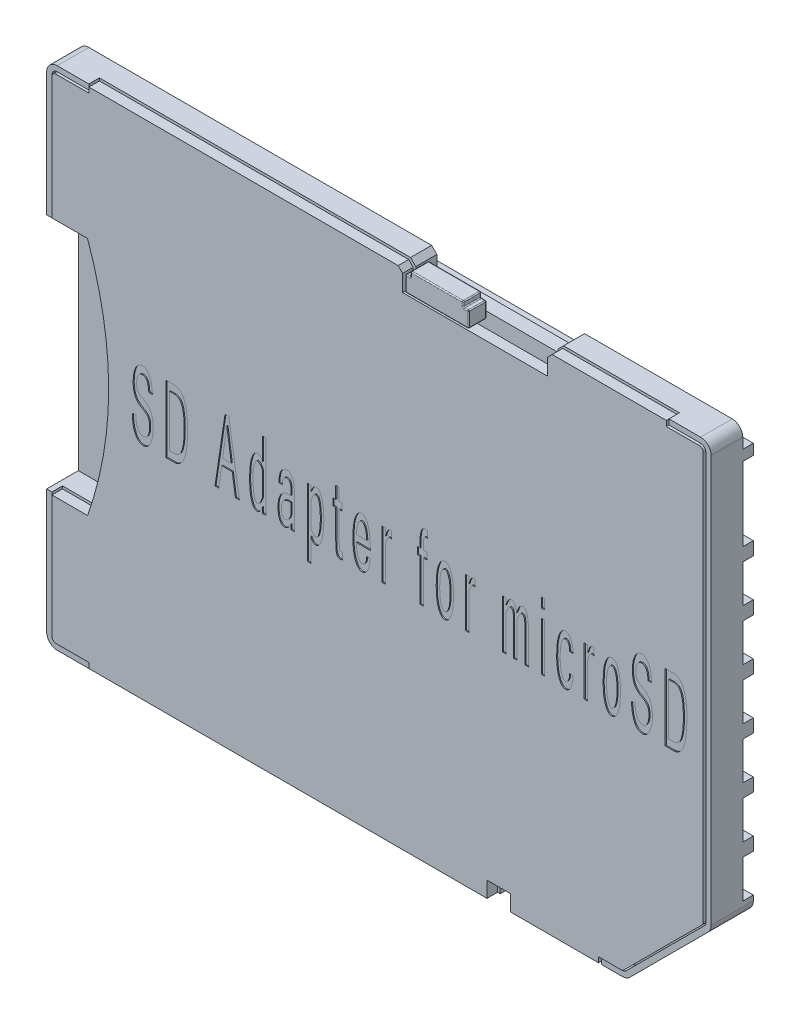
SolidWorks part; units mm, degrees
ref_plane "Front Plane" through (0, 0, 0) normal (0, 0, 1) x (1, 0, 0)
ref_plane "Top Plane" through (0, 0, 0) normal (0, 1, 0) x (1, 0, 0)
ref_plane "Right Plane" through (0, 0, 0) normal (1, 0, 0) x (0, 0, -1)
sketch "Sketch1" plane through (0, 0, 0) normal (0, 0, 1) x (1, 0, 0)
  line L0 (6.25, 0) -> (6.25, 0.75)
  line L1 (15.75, 24) -> (15.75, 4)
  line L2 (-15.75, 0) -> (-15.75, 24)
  line L3 (11.75, 0) -> (6.25, 0)
  line L4 (6.25, 0.75) -> (5.25, 0.75)
  line L5 (15.75, 4) -> (11.75, 0)
  line L6 (5.25, 0.75) -> (5.25, 0)
  line L7 (5.25, 0) -> (-15.75, 0)
  line L8 (-15.75, 24) -> (15.75, 24)
extrude "Boss-Extrude1" add sketch "Sketch1" along normal blind 2
fillet "Fillet1" radius 0.5 5 edges at (-15.75, 0, 1) (-15.75, 24, 1) (15.75, 24, 1) (11.75, 0, 1) (15.75, 4, 1)
sketch "Sketch2" plane through (0, 0, 0) normal (0, 0, -1) x (-1, 0, 0)
  line L0 (15.75, 23) -> (15.75, 23.5)
  line L2 (0, 23) -> (15.75, 23)
  line L3 (15.75, 23.5) -> (15.75, 0.5) construction
  line L4 (0, 23) -> (-15.75, 23)
  line L5 (-15.75, 4.2071) -> (-15.75, 23.5) construction
  line L6 (-15.75, 23) -> (-15.75, 23.5)
  line L10 (15.25, 24) -> (-15.25, 24)
  line L11 (15.25, 24) -> (-15.25, 24)
  arc A6 (15.75, 23.5) -> (15.25, 24) centre (15.25, 23.5) ccw
  arc A7 (-15.25, 24) -> (-15.75, 23.5) centre (-15.25, 23.5) ccw
  arc A8 (15.75, 23.5) -> (15.25, 24) centre (15.25, 23.5) ccw
  arc A9 (-15.25, 24) -> (-15.75, 23.5) centre (-15.25, 23.5) ccw
  dimension "D1" = 0
extrude "Cut-Extrude1" cut sketch "Sketch2" against normal blind 0.5
sketch "Sketch3" plane through (0, 0, 0) normal (0, 0, -1) x (-1, 0, 0)
  line L1 (0, 0.75) -> (15.75, 0.75)
  line L2 (15.75, 23) -> (15.75, 0.5) construction
  line L3 (15.75, 0.75) -> (15.75, 0.5)
  line L4 (0, 0.75) -> (-12.5, 0.75)
  line L5 (-11.8964, 0.1464) -> (-15.6036, 3.8536) construction
  line L6 (-12.5, 0.75) -> (-11.8964, 0.1464)
  line L18 (15.25, 0) -> (-5.25, 0)
  line L19 (15.25, 0) -> (-5.25, 0)
  line L20 (-6.25, 0) -> (-5.25, 0)
  line L21 (-11.5429, 0) -> (-6.25, 0)
  line L22 (-11.5429, 0) -> (-6.25, 0)
  arc A16 (15.25, 0) -> (15.75, 0.5) centre (15.25, 0.5) ccw
  arc A17 (15.25, 0) -> (15.75, 0.5) centre (15.25, 0.5) ccw
  arc A20 (-11.8964, 0.1464) -> (-11.5429, 0) centre (-11.5429, 0.5) ccw
  arc A21 (-11.8964, 0.1464) -> (-11.5429, 0) centre (-11.5429, 0.5) ccw
  dimension "D1" = 0
  dimension "D2" = 0
extrude "Cut-Extrude2" cut sketch "Sketch3" against normal blind 0.5
sketch "Sketch4" plane through (0, 0, 2) normal (0, 0, 1) x (1, 0, 0)
  line L0 (1.25, 23.25) -> (8, 23.25)
  line L1 (1.25, 24) -> (1.25, 23.25)
  line L2 (15.25, 24) -> (-15.25, 24) construction
  line L3 (8, 23.25) -> (8, 24)
  line L4 (1.25, 24) -> (8, 24)
extrude "Cut-Extrude3" cut sketch "Sketch4" against normal blind 1.5
chamfer "Chamfer1" distance 0.25 angle 45 2 edges at (8, 24, 1.25) (1.25, 24, 1.25)
sketch "Sketch5" plane through (0, 0, 0) normal (0, 0, -1) x (-1, 0, 0)
  line L0 (-15.75, 23) -> (-15.75, 22.5)
  line L1 (-15.75, 4.2071) -> (-15.75, 23) construction
  line L2 (-15.75, 22.5) -> (-10, 22.5)
  line L3 (-10, 22.5) -> (-10, 19)
  line L4 (-10, 19) -> (-15.75, 19)
  line L5 (-15.75, 19) -> (-15.75, 22.5)
  line M5 (-15.75, 23) -> (-15.75, 4.2071)
extrude "Cut-Extrude4" cut sketch "Sketch5" against normal blind 0.5 contours L4 L3 L2 M5
sketch "Sketch9" plane through (0, 0, 0) normal (0, 0, -1) x (-1, 0, 0)
  line L0 (-15.75, 18.375) -> (-15.75, 16.575)
  line L1 (-15.75, 4.2071) -> (-15.75, 19) construction
  line L2 (-15.75, 18.375) -> (-10, 18.375)
  line L3 (-10, 18.375) -> (-10, 16.575)
  line L4 (-10, 16.575) -> (-15.75, 16.575)
  line L5 (-15.75, 6.25) -> (-15.75, 4.45)
  line L6 (-15.75, 15.95) -> (-10, 15.95)
  line L7 (-10, 15.95) -> (-10, 14.15)
  line L8 (-10, 14.15) -> (-15.75, 14.15)
  line L9 (-15.75, 8.675) -> (-15.75, 6.875)
  line L10 (-15.75, 13.525) -> (-10, 13.525)
  line L11 (-10, 13.525) -> (-10, 11.725)
  line L12 (-10, 11.725) -> (-15.75, 11.725)
  line L13 (-15.75, 11.1) -> (-15.75, 9.3)
  line L14 (-15.75, 11.1) -> (-10, 11.1)
  line L15 (-10, 11.1) -> (-10, 9.3)
  line L16 (-10, 9.3) -> (-15.75, 9.3)
  line L17 (-15.75, 13.525) -> (-15.75, 11.725)
  line L18 (-15.75, 8.675) -> (-10, 8.675)
  line L19 (-10, 8.675) -> (-10, 6.875)
  line L20 (-10, 6.875) -> (-15.75, 6.875)
  line L21 (-15.75, 15.95) -> (-15.75, 14.15)
  line L22 (-15.75, 6.25) -> (-10, 6.25)
  line L23 (-10, 6.25) -> (-10, 4.45)
  line L24 (-10, 4.45) -> (-15.75, 4.45)
  line L26 (-15.6, 3.85) -> (-7.75, 3.85)
  line L27 (-7.75, 3.85) -> (-7.75, 2.05)
  line L28 (-7.75, 2.05) -> (-13.8, 2.05)
  line L29 (-12.5, 0.75) -> (-15.6036, 3.8536) construction
  line L30 (-13.8, 2.05) -> (-15.6, 3.85)
  dimension "D1" = 1.8
  dimension "D2" = 1.8
  dimension "D3" = 1.8
  dimension "D4" = 1.8
  dimension "D5" = 1.8
  dimension "D6" = 1.8
  dimension "D7" = 0.625
  dimension "D8" = 0.625
  dimension "D9" = 0.625
  dimension "D10" = 0.625
  dimension "D11" = 0.625
extrude "Cut-Extrude7" cut sketch "Sketch9" against normal blind 0.5
sketch "Sketch10" plane through (0, 0, 0.5) normal (0, 0, -1) x (-1, 0, 0)
  line L6 (-10.125, 22.5) -> (-10.125, 19)
  line L7 (-10.125, 22.375) -> (-10.125, 19.125)
  line L9 (-10.125, 16.575) -> (-10.125, 18.375)
  line L10 (-10.125, 16.7) -> (-10.125, 18.25)
  line L12 (-10.125, 14.15) -> (-10.125, 15.95)
  line L13 (-10.125, 14.275) -> (-10.125, 15.825)
  line L15 (-10.125, 11.725) -> (-10.125, 13.525)
  line L16 (-10.125, 11.85) -> (-10.125, 13.4)
  line L18 (-10.125, 9.3) -> (-10.125, 11.1)
  line L19 (-10.125, 9.425) -> (-10.125, 10.975)
  line L21 (-10.125, 6.875) -> (-10.125, 8.675)
  line L22 (-10.125, 7) -> (-10.125, 8.55)
  line L24 (-10.125, 4.45) -> (-10.125, 6.25)
  line L25 (-10.125, 4.575) -> (-10.125, 6.125)
  line L26 (-14.125, 22.375) -> (-14.125, 19.125)
  line L27 (-7.875, 2.05) -> (-7.875, 3.85)
  line L28 (-7.875, 2.175) -> (-7.875, 3.725)
  line L29 (-14.125, 16.7) -> (-14.125, 18.25)
  line L30 (-14.125, 14.275) -> (-14.125, 15.825)
  line L31 (-14.125, 11.85) -> (-14.125, 13.4)
  line L32 (-14.125, 9.425) -> (-14.125, 10.975)
  line L33 (-14.125, 7) -> (-14.125, 8.55)
  line L34 (-14.125, 4.575) -> (-14.125, 6.125)
  line L37 (-15.75, 22.375) -> (-10, 22.375)
  line L38 (-14.125, 22.375) -> (-10.125, 22.375)
  line L40 (-10, 19.125) -> (-15.75, 19.125)
  line L41 (-10.125, 19.125) -> (-14.125, 19.125)
  line L43 (-10, 18.25) -> (-15.75, 18.25)
  line L44 (-10.125, 18.25) -> (-14.125, 18.25)
  line L46 (-15.75, 16.7) -> (-10, 16.7)
  line L47 (-14.125, 16.7) -> (-10.125, 16.7)
  line L52 (-10, 15.825) -> (-15.75, 15.825)
  line L53 (-10.125, 15.825) -> (-14.125, 15.825)
  line L55 (-15.75, 14.275) -> (-10, 14.275)
  line L56 (-14.125, 14.275) -> (-10.125, 14.275)
  line L58 (-10, 13.4) -> (-15.75, 13.4)
  line L59 (-10.125, 13.4) -> (-14.125, 13.4)
  line L61 (-15.75, 11.85) -> (-10, 11.85)
  line L62 (-14.125, 11.85) -> (-10.125, 11.85)
  line L64 (-10, 10.975) -> (-15.75, 10.975)
  line L65 (-10.125, 10.975) -> (-14.125, 10.975)
  line L67 (-15.75, 9.425) -> (-10, 9.425)
  line L68 (-14.125, 9.425) -> (-10.125, 9.425)
  line L70 (-10, 8.55) -> (-15.75, 8.55)
  line L71 (-10.125, 8.55) -> (-14.125, 8.55)
  line L73 (-15.75, 7) -> (-10, 7)
  line L74 (-14.125, 7) -> (-10.125, 7)
  line L76 (-10, 6.125) -> (-15.75, 6.125)
  line L77 (-10.125, 6.125) -> (-14.125, 6.125)
  line L79 (-15.75, 4.575) -> (-10, 4.575)
  line L80 (-14.125, 4.575) -> (-10.125, 4.575)
  line L82 (-7.75, 3.725) -> (-15.6, 3.725)
  line L83 (-7.875, 3.725) -> (-11.625, 3.725)
  line L84 (-11.625, 2.175) -> (-11.625, 3.725)
  line L85 (-13.8, 2.175) -> (-7.75, 2.175)
  line L86 (-11.625, 2.175) -> (-7.875, 2.175)
  line L88 (-11.625, 2.05) -> (-11.625, 3.85) construction
  line L89 (-7.875, 2.05) -> (-7.875, 3.85) construction
  line L90 (-14.125, 4.45) -> (-14.125, 6.25) construction
  line L91 (-10.125, 4.45) -> (-10.125, 6.25) construction
  line L92 (-14.125, 6.875) -> (-14.125, 8.675) construction
  line L93 (-10.125, 6.875) -> (-10.125, 8.675) construction
  line L94 (-14.125, 9.3) -> (-14.125, 11.1) construction
  line L95 (-10.125, 9.3) -> (-10.125, 11.1) construction
  line L96 (-14.125, 11.725) -> (-14.125, 13.525) construction
  line L97 (-10.125, 11.725) -> (-10.125, 13.525) construction
  line L98 (-14.125, 14.15) -> (-14.125, 15.95) construction
  line L99 (-10.125, 14.15) -> (-10.125, 15.95) construction
  line L100 (-14.125, 16.575) -> (-14.125, 18.375) construction
  line L101 (-10.125, 16.575) -> (-10.125, 18.375) construction
  line L102 (-14.125, 22.5) -> (-14.125, 19) construction
  line L103 (-10.125, 22.5) -> (-10.125, 19) construction
  dimension "D1" = 0.125
  dimension "D2" = 0.125
  dimension "D3" = 0.125
  dimension "D4" = 0.125
  dimension "D5" = 0.125
  dimension "D6" = 0.125
  dimension "D7" = 0.125
  dimension "D8" = 0.125
  dimension "D9" = 4
  dimension "D10" = 4
  dimension "D11" = 0.125
  dimension "D12" = 0.125
  dimension "D13" = 0.125
  dimension "D14" = 0.125
  dimension "D15" = 0.125
  dimension "D16" = 0.125
  dimension "D17" = 0.125
  dimension "D18" = 0.125
  dimension "D19" = 0.125
  dimension "D20" = 0.125
  dimension "D21" = 0.125
  dimension "D22" = 0.125
  dimension "D23" = 0.125
  dimension "D24" = 0.125
  dimension "D25" = 0.125
  dimension "D26" = 0.125
  dimension "D27" = 3.75
extrude "Boss-Extrude2" add sketch "Sketch10" along normal blind 0.05 separate body
sketch "Sketch11" plane through (0, 23.25, 0) normal (0, 1, 0) x (1, 0, 0)
  line L0 (8, -1.9) -> (8, -1.15)
  line L1 (8, -0.5) -> (8, -2) construction
  line L2 (8, -1.9) -> (1.25, -1.9)
  line L3 (1.25, -0.5) -> (1.25, -2) construction
  line L4 (1.25, -1.9) -> (1.25, -1.15)
  line L5 (1.25, -0.5) -> (1.25, -2) construction
  line L6 (1.25, -1.15) -> (8, -1.15)
  line L7 (8, -2) -> (8, -0.5) construction
  line L8 (8, -1.15) -> (8, -1.9)
  line M4 (8, -2) -> (8, -0.5)
  line M6 (1.25, -0.5) -> (1.25, -2)
extrude "Cut-Extrude8" cut sketch "Sketch11" against normal blind 0.25 contours L6 L2 M6 M4
sketch "Sketch12" plane through (0, 0, 2) normal (0, 0, 1) x (1, 0, 0)
  line L15 (-15.75, 6.375) -> (-15.75, 17.625)
  line L16 (-15.75, 6.375) -> (-13.75, 6.375)
  line L17 (-15.75, 17.625) -> (-13.75, 17.625)
  spline S0 degree 2 poles (-13.75, 6.375) (-12.25, 12) (-13.75, 17.625) knots 0 0 0 1 1 1
extrude "Cut-Extrude9" cut sketch "Sketch12" against normal blind 1.5
sketch "Sketch13" plane through (0, 0, 2) normal (0, 0, 1) x (1, 0, 0)
  line L2 (-15.5, 23.5) -> (-15.5, 17.625)
  line L3 (-15.5, 23.5) -> (-15.5, 17.625)
  line L4 (-13.75, 24) -> (1, 24)
  line L5 (1, 23.75) -> (-15.25, 23.75)
  line L6 (-13.75, 23.75) -> (-15.25, 23.75)
  line L7 (-13.75, 23.75) -> (-13.75, 24)
  line L8 (1, 24) -> (-15.25, 24) construction
  line L9 (1, 24) -> (1.25, 23.75)
  line L10 (1.25, 23.75) -> (1.25, 23.25)
  line L11 (1.25, 23.25) -> (8, 23.25)
  line L12 (8, 23.25) -> (8, 23.75)
  line L13 (8, 23.75) -> (8.25, 24)
  line L16 (15.5, 4.2071) -> (15.5, 23.5)
  line L17 (15.5, 4.2071) -> (15.5, 23.5)
  line L19 (11.7197, 0.3232) -> (15.4268, 4.0303)
  line L20 (11.7197, 0.3232) -> (15.4268, 4.0303)
  line L38 (11.5429, 0.25) -> (10.5429, 0.25)
  line L39 (10.5429, 0.25) -> (10.5429, 0)
  line L40 (6.25, 0) -> (11.5429, 0) construction
  line L41 (10.5429, 0) -> (6.25, 0)
  line L42 (6.25, 0) -> (6.25, 0.75)
  line L43 (6.25, 0.75) -> (5.25, 0.75)
  line L44 (5.25, 0.75) -> (5.25, 0)
  line L46 (-13.75, 0) -> (5.25, 0)
  line L47 (-15.5, 6.375) -> (-15.5, 0.5)
  line L48 (-15.5, 6.375) -> (-15.5, 0.5)
  line L49 (-13.75, 0.25) -> (-13.75, 0)
  line L50 (-15.25, 0) -> (5.25, 0) construction
  line L51 (-15.25, 0.25) -> (-13.75, 0.25)
  line L52 (13.75, 24) -> (8.25, 24)
  line L53 (13.75, 23.75) -> (13.75, 24)
  line L54 (15.25, 24) -> (8.25, 24) construction
  line L55 (15.25, 23.75) -> (13.75, 23.75)
  line L58 (-13.75, 17.625) -> (-15.75, 17.625)
  line L59 (-13.75, 17.625) -> (-15.5, 17.625)
  line L61 (-15.75, 6.375) -> (-13.75, 6.375)
  line L62 (-15.5, 6.375) -> (-13.75, 6.375)
  arc A2 (-15.25, 23.75) -> (-15.5, 23.5) centre (-15.25, 23.5) ccw
  arc A3 (-15.25, 23.75) -> (-15.5, 23.5) centre (-15.25, 23.5) ccw
  arc A5 (15.5, 23.5) -> (15.25, 23.75) centre (15.25, 23.5) ccw
  arc A6 (15.5, 23.5) -> (15.25, 23.75) centre (15.25, 23.5) ccw
  arc A8 (15.4268, 4.0303) -> (15.5, 4.2071) centre (15.25, 4.2071) ccw
  arc A9 (15.4268, 4.0303) -> (15.5, 4.2071) centre (15.25, 4.2071) ccw
  arc A16 (11.5429, 0.25) -> (11.7197, 0.3232) centre (11.5429, 0.5) ccw
  arc A17 (11.5429, 0.25) -> (11.7197, 0.3232) centre (11.5429, 0.5) ccw
  arc A19 (-15.5, 0.5) -> (-15.25, 0.25) centre (-15.25, 0.5) ccw
  arc A20 (-15.5, 0.5) -> (-15.25, 0.25) centre (-15.25, 0.5) ccw
  parabola Q3 (-13.75, 6.375) -> (-13.75, 17.625) focus (-23.5469, 12) apex (-13, 12)
  parabola Q4 (-13.75, 6.375) -> (-13.75, 17.625) focus (-23.5469, 12) apex (-13, 12)
  dimension "D4" = 0.25
  dimension "D9" = 0.25
  dimension "D11" = 0
  dimension "D1" = 0.25
  dimension "D2" = 0.25
  dimension "D3" = 0.25
  dimension "D5" = 0.25
  dimension "D6" = 0.25
  dimension "D7" = 0.25
  dimension "D8" = 0.25
  dimension "D10" = 0.25
  dimension "D12" = 0
  dimension "D13" = 0
extrude "Cut-Extrude11" cut sketch "Sketch13" against normal blind 0.5
sketch "Sketch14" plane through (0, 0, 1.5) normal (0, 0, 1) x (1, 0, 0)
  line L0 (-13.75, 17.625) -> (-3.75, 17.625)
  line L1 (-3.75, 17.625) -> (-3.75, 6.375)
  line L2 (-13.75, 6.375) -> (-3.75, 6.375)
  parabola Q2 (-13.75, 6.375) -> (-13.75, 17.625) focus (-23.5469, 12) apex (-13, 12)
  parabola Q3 (-13.75, 6.375) -> (-13.75, 17.625) focus (-23.5469, 12) apex (-13, 12)
  dimension "D1" = 0
extrude "Cut-Extrude12" cut sketch "Sketch14" against normal blind 1
ref_plane "Plane1" through (0, 0, 1.5625) normal (0, 0, 1) x (1, 0, 0)
sketch "Sketch16" plane through (0, 0, 1.5625) normal (0, 0, 1) x (1, 0, 0)
  line L54 (-15.4375, 17.6875) -> (-3.6875, 17.6875)
  line L55 (-3.6875, 17.6875) -> (-3.6875, 6.3125)
  line L56 (-3.6875, 6.3125) -> (-15.4375, 6.3125)
  line L57 (-15.4375, 6.3125) -> (-15.4375, 0.5)
  line L58 (-15.25, 0.3125) -> (-13.6875, 0.3125)
  line L59 (-13.6875, 0.3125) -> (-13.6875, 0.0625)
  line L60 (-13.6875, 0.0625) -> (5.1875, 0.0625)
  line L61 (5.1875, 0.0625) -> (5.1875, 0.8125)
  line L62 (5.1875, 0.8125) -> (6.3125, 0.8125)
  line L63 (6.3125, 0.8125) -> (6.3125, 0.0625)
  line L64 (6.3125, 0.0625) -> (10.4804, 0.0625)
  line L65 (10.4804, 0.0625) -> (10.4804, 0.3125)
  line L66 (10.4804, 0.3125) -> (11.5429, 0.3125)
  line L67 (11.6755, 0.3674) -> (15.3826, 4.0745)
  line L68 (15.4375, 4.2071) -> (15.4375, 23.5)
  line L69 (15.25, 23.6875) -> (13.6875, 23.6875)
  line L70 (13.6875, 23.6875) -> (13.6875, 23.9375)
  line L71 (13.6875, 23.9375) -> (8.2759, 23.9375)
  line L72 (8.2759, 23.9375) -> (8.0625, 23.7241)
  line L73 (8.0625, 23.7241) -> (8.0625, 22.9375)
  line L74 (8.0625, 22.9375) -> (1.1875, 22.9375)
  line L75 (1.1875, 22.9375) -> (1.1875, 23.7241)
  line L76 (1.1875, 23.7241) -> (0.9741, 23.9375)
  line L77 (0.9741, 23.9375) -> (-13.6875, 23.9375)
  line L78 (-13.6875, 23.9375) -> (-13.6875, 23.6875)
  line L79 (-13.6875, 23.6875) -> (-15.25, 23.6875)
  line L80 (-15.4375, 23.5) -> (-15.4375, 17.6875)
  line L81 (-15.4375, 17.6875) -> (-13.75, 17.6875)
  line L83 (-13.75, 6.3125) -> (-15.4375, 6.3125)
  line L84 (-15.4375, 6.3125) -> (-15.4375, 0.5)
  line L85 (-15.25, 0.3125) -> (-13.6875, 0.3125)
  line L86 (-13.6875, 0.3125) -> (-13.6875, 0.0625)
  line L87 (-13.6875, 0.0625) -> (5.1875, 0.0625)
  line L88 (5.1875, 0.0625) -> (5.1875, 0.8125)
  line L89 (5.1875, 0.8125) -> (6.3125, 0.8125)
  line L90 (6.3125, 0.8125) -> (6.3125, 0.0625)
  line L91 (6.3125, 0.0625) -> (10.4804, 0.0625)
  line L92 (10.4804, 0.0625) -> (10.4804, 0.3125)
  line L93 (10.4804, 0.3125) -> (11.5429, 0.3125)
  line L94 (11.6755, 0.3674) -> (15.3826, 4.0745)
  line L95 (15.4375, 4.2071) -> (15.4375, 23.5)
  line L96 (15.25, 23.6875) -> (13.6875, 23.6875)
  line L97 (13.6875, 23.6875) -> (13.6875, 23.9375)
  line L98 (13.6875, 23.9375) -> (8.2759, 23.9375)
  line L99 (8.2759, 23.9375) -> (8.0625, 23.7241)
  line L100 (8.0625, 23.7241) -> (8.0625, 22.9375)
  line L101 (8.0625, 22.9375) -> (1.1875, 22.9375)
  line L102 (1.1875, 22.9375) -> (1.1875, 23.7241)
  line L103 (1.1875, 23.7241) -> (0.9741, 23.9375)
  line L104 (0.9741, 23.9375) -> (-13.6875, 23.9375)
  line L105 (-13.6875, 23.9375) -> (-13.6875, 23.6875)
  line L106 (-13.6875, 23.6875) -> (-15.25, 23.6875)
  line L107 (-15.4375, 23.5) -> (-15.4375, 17.6875)
  arc A10 (-15.4375, 0.5) -> (-15.25, 0.3125) centre (-15.25, 0.5) ccw
  arc A11 (11.5429, 0.3125) -> (11.6755, 0.3674) centre (11.5429, 0.5) ccw
  arc A12 (15.3826, 4.0745) -> (15.4375, 4.2071) centre (15.25, 4.2071) ccw
  arc A13 (15.4375, 23.5) -> (15.25, 23.6875) centre (15.25, 23.5) ccw
  arc A14 (-15.25, 23.6875) -> (-15.4375, 23.5) centre (-15.25, 23.5) ccw
  arc A15 (-15.4375, 0.5) -> (-15.25, 0.3125) centre (-15.25, 0.5) ccw
  arc A16 (11.5429, 0.3125) -> (11.6755, 0.3674) centre (11.5429, 0.5) ccw
  arc A17 (15.3826, 4.0745) -> (15.4375, 4.2071) centre (15.25, 4.2071) ccw
  arc A18 (15.4375, 23.5) -> (15.25, 23.6875) centre (15.25, 23.5) ccw
  arc A19 (-15.25, 23.6875) -> (-15.4375, 23.5) centre (-15.25, 23.5) ccw
  spline S0 degree 2 poles (-13.75, 6.3125) (-11.75, 12) (-13.75, 17.6875) knots 0 0 0 1 1 1
  dimension "D1" = 0.0625
extrude "Boss-Extrude3" add sketch "Sketch16" along normal blind 0.5 separate body
sketch "Sketch19" plane through (0, 0, 2.0625) normal (0, 0, 1) x (1, 0, 0)
  text T0 "SD Adapter for microSD" font "Microsoft Sans Serif" height 3.175
extrude "Cut-Extrude13" cut sketch "Sketch19" against normal blind 0.05
sketch "Sketch20" plane through (0, 23, 0) normal (0, 1, 0) x (1, 0, 0)
  line L8 (1.25, -1.15) -> (1.25, -1.5)
  line L9 (1.25, -1.5) -> (8, -1.5)
  line L10 (8, -1.5) -> (8, -1.15)
  line L11 (8, -1.15) -> (1.25, -1.15)
  line L12 (1.25, -1.15) -> (1.25, -1.5)
  line L13 (1.25, -1.5) -> (8, -1.5)
  line L14 (8, -1.5) -> (8, -1.15)
  line L15 (8, -1.15) -> (1.25, -1.15)
  dimension "D1" = 0
extrude "Cut-Extrude14" cut sketch "Sketch20" against normal blind 1
ref_plane "Plane2" through (0, 23, 0) normal (0, 1, 0) x (1, 0, 0)
sketch "Sketch22" plane through (0, 23, 0) normal (0, 1, 0) x (1, 0, 0)
  line L2 (1.3125, -1.15) -> (1.3125, -1.5)
  line L3 (1.3125, -1.2125) -> (1.3125, -1.5)
  line L4 (1.3125, -1.5) -> (1.3125, -2.0625)
  line L5 (8, -1.2125) -> (1.25, -1.2125)
  line L6 (4.3125, -1.2125) -> (1.3125, -1.2125)
  line L7 (8.0625, -2.0625) -> (1.1875, -2.0625) construction
  line L8 (1.3125, -2.0625) -> (4.3125, -2.0625)
  line L9 (4.3125, -2.0625) -> (4.3125, -1.2125)
  dimension "D1" = 0.0625
  dimension "D2" = 0.0625
extrude "Boss-Extrude4" add sketch "Sketch22" along normal blind 1 separate body
sketch "Sketch23" plane through (0, 0, 2.0625) normal (0, 0, 1) x (1, 0, 0)
  line L1 (1.3125, 24) -> (1.5625, 24)
  line L2 (1.3125, 24) -> (1.3125, 23.75)
  line L3 (1.3125, 23.75) -> (1.5625, 23.75)
  line L4 (1.5625, 24) -> (1.5625, 23.75)
  line L5 (4.3125, 24) -> (4.0625, 24)
  line L6 (4.3125, 24) -> (4.3125, 23.75)
  line L7 (4.3125, 23.75) -> (4.0625, 23.75)
  line L8 (4.0625, 24) -> (4.0625, 23.75)
extrude "Cut-Extrude15" cut sketch "Sketch23" against normal blind 1
fillet "Fillet3" radius 0.05 24 edges at (2.8125, 23, 1.2125) (1.3125, 23, 1.6375) (1.3125, 23.375, 1.2125) (1.4375, 23.75, 1.2125) (1.3125, 23.75, 1.6375) (1.5625, 23.875, 1.2125) (1.5625, 23.75, 1.6375) (2.8125, 24, 1.2125) (1.5625, 24, 1.6375) (4.3125, 23, 1.6375) (4.3125, 23.375, 1.2125) (4.0625, 23.875, 1.2125) (4.0625, 24, 1.6375) (4.1875, 23.75, 1.2125) (4.3125, 23.75, 1.6375) (4.0625, 23.75, 1.6375) (4.0625, 23.875, 2.0625) (4.1875, 23.75, 2.0625) (4.3125, 23.375, 2.0625) (2.8125, 23, 2.0625) (1.3125, 23.375, 2.0625) (1.4375, 23.75, 2.0625) (1.5625, 23.875, 2.0625) (2.8125, 24, 2.0625)
